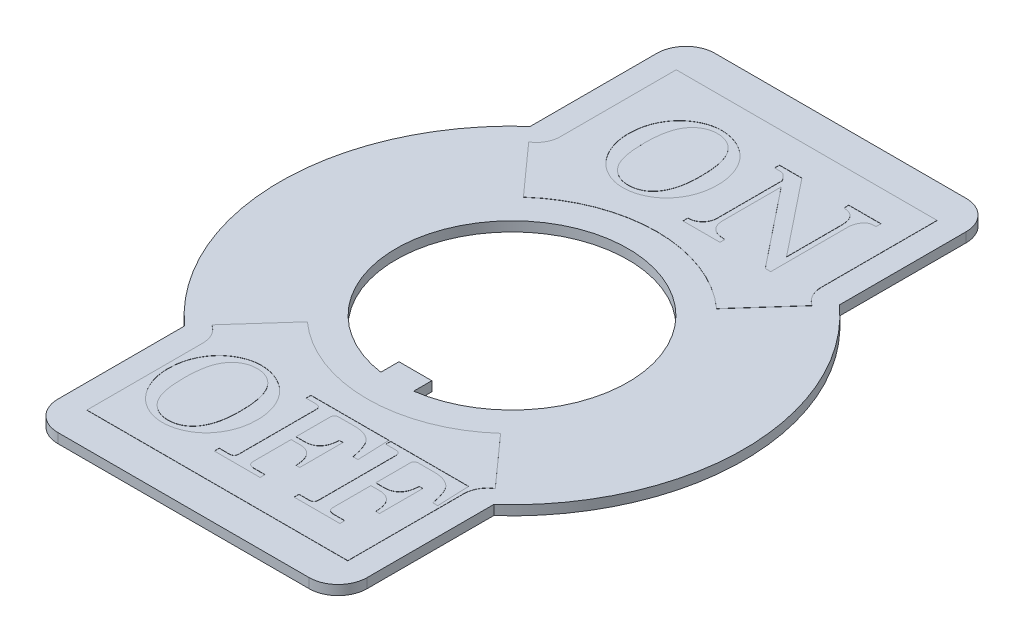
SolidWorks part; units mm, degrees
material "7075-T6, Plate (SS)"
ref_plane "Front Plane" through (0, 0, 0) normal (0, 0, 1) x (1, 0, 0)
ref_plane "Top Plane" through (0, 0, 0) normal (0, 1, 0) x (1, 0, 0)
ref_plane "Right Plane" through (0, 0, 0) normal (1, 0, 0) x (0, 0, -1)
sketch "Sketch1" plane through (0, 0, 0) normal (0, 1, 0) x (1, 0, 0)
  line L0 (0, 0) -> (0, -6) construction
  line L1 (6.5, 17) -> (-6.5, 17)
  line L2 (8, 15.5) -> (8, -15.5)
  line L3 (6.5, -17) -> (-6.5, -17)
  line L4 (-8, 15.5) -> (-8, -15.5)
  line L5 (8, 17) -> (-8, -17) construction
  line L6 (8, -17) -> (-8, 17) construction
  line L8 (0.85, -5) -> (-0.85, -5)
  line L9 (0.85, -5) -> (0.85, -7)
  line L10 (0.85, -7) -> (-0.85, -7)
  line L11 (-0.85, -5) -> (-0.85, -7)
  line L12 (0.85, -5) -> (-0.85, -7) construction
  line L13 (0.85, -7) -> (-0.85, -5) construction
  circle A0 centre (0, 0) radius 6
  circle A1 centre (0, 0) radius 12
  arc A2 (8, -15.5) -> (6.5, -17) centre (6.5, -15.5) cw
  arc A3 (-6.5, -17) -> (-8, -15.5) centre (-6.5, -15.5) cw
  arc A4 (-6.5, 17) -> (-8, 15.5) centre (-6.5, 15.5) ccw
  arc A5 (6.5, 17) -> (8, 15.5) centre (6.5, 15.5) cw
  dimension "D1" = 12
  dimension "D2" = 24
  dimension "D7" = 1.5
  dimension "D3" = 34
  dimension "D4" = 16
  dimension "D5" = 1.7
  dimension "D6" = 2
extrude "Boss-Extrude1" add sketch "Sketch1" along normal blind 0.5 contours A1 L2 L1 L4 | L2 A1 L4 A0 L9 L10 L11 | A1 L4 L3 L2 | L11 A0 L9 L8 | A0 L11 L10 L9 | L4 A1 | L2 A1
sketch "Sketch2" plane through (0, 0.5, 0) normal (0, 1, 0) x (1, 0, 0)
  line L0 (6.75, 15.25) -> (-6.75, 15.25)
  line L1 (-6.75, 15.25) -> (-6.75, 9.25)
  line L2 (-7.3333, 8.1989) -> (-5, 5.5902)
  line L3 (0, 0) -> (0, 7.5) construction
  line L4 (0, 0) -> (-6, 0) construction
  line L5 (7.3333, 8.1989) -> (5, 5.5902)
  line L6 (6.75, 15.25) -> (6.75, 9.25)
  line L7 (6.75, -15.25) -> (6.75, -9.25)
  line L8 (7.3333, -8.1989) -> (5, -5.5902)
  line L9 (-7.3333, -8.1989) -> (-5, -5.5902)
  line L10 (-6.75, -15.25) -> (-6.75, -9.25)
  line L11 (6.75, -15.25) -> (-6.75, -15.25)
  line L12 (-5, 5.5902) -> (0, 0) construction
  arc A0 (-5, 5.5902) -> (5, 5.5902) centre (0, 0) cw
  arc A1 (-6.75, 9.25) -> (-7.3333, 8.1989) centre (-7.9886, 9.25) cw
  arc A2 (0.85, -5.9395) -> (-0.85, -5.9395) centre (0, 0) ccw construction
  arc A3 (6.75, 9.25) -> (7.3333, 8.1989) centre (7.9886, 9.25) ccw
  arc A4 (6.75, -9.25) -> (7.3333, -8.1989) centre (7.9886, -9.25) cw
  arc A5 (-6.75, -9.25) -> (-7.3333, -8.1989) centre (-7.9886, -9.25) ccw
  arc A6 (-5, -5.5902) -> (5, -5.5902) centre (0, 0) ccw
  point P8 (0, 15.25)
  point P10 (0, 7.5)
  point P30 (0, -15.25)
  dimension "D1" = 13.5
  dimension "D6" = 7.5
  dimension "D2" = 6
  dimension "D3" = 3.5
  dimension "D4" = 10
  dimension "D5" = 30.5
extrude "Boss-Extrude2" add sketch "Sketch2" along normal blind 0.01
sketch "Sketch3" plane through (0, 0.51, 0) normal (0, 1, 0) x (1, 0, 0)
  line L0 (-6.9056, 8.6489) -> (6.9056, 8.6489) construction
  line L1 (-6.9056, -13.7909) -> (6.75, -13.7909) construction
  line L3 (6.75, -15.25) -> (6.75, -9.25) construction
  arc A0 (-7.3333, 8.1989) -> (-6.75, 9.25) centre (-7.9886, 9.25) ccw construction
  arc A1 (6.75, 9.25) -> (7.3333, 8.1989) centre (7.9886, 9.25) ccw construction
  text T0 "ON" font "Century Schoolbook" height 5
  text T1 "OFF" font "Century Schoolbook" height 5
  point P11 (-6.9056, -13.7909)
  point P15 (0, 0)
extrude "Cut-Extrude1" cut sketch "Sketch3" against normal blind 0.01
